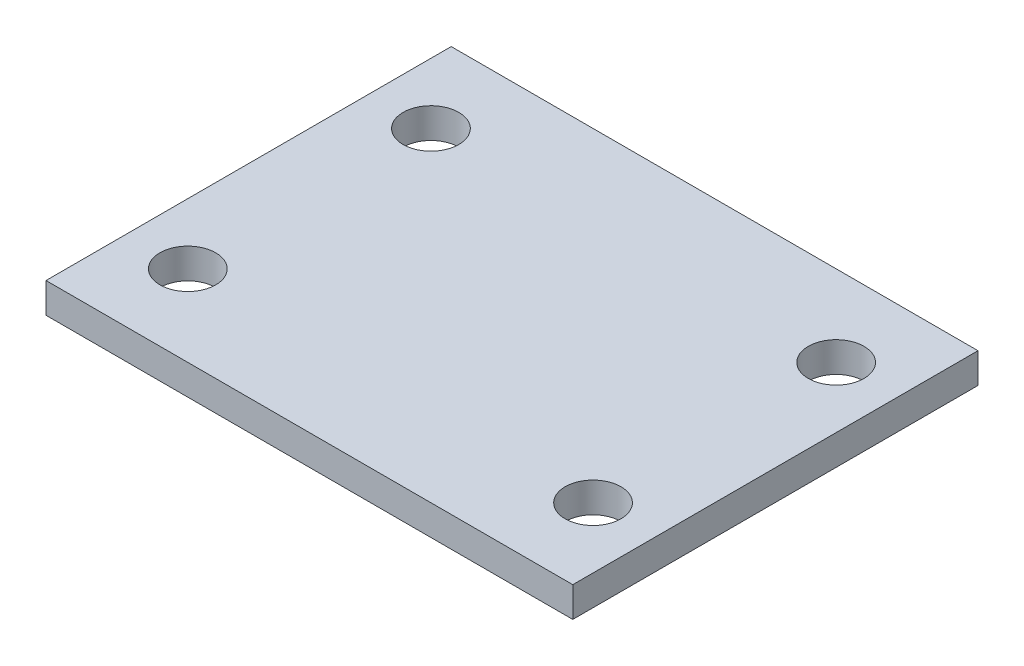
SolidWorks part; units mm, degrees
ref_plane "Front Plane" through (0, 0, 0) normal (0, 0, 1) x (1, 0, 0)
ref_plane "Top Plane" through (0, 0, 0) normal (0, 1, 0) x (1, 0, 0)
ref_plane "Right Plane" through (0, 0, 0) normal (1, 0, 0) x (0, 0, -1)
sketch "Sketch1" plane through (0, 0, 0) normal (0, 1, 0) x (1, 0, 0)
  line L1 (-26, 20) -> (26, 20)
  line L2 (-26, 20) -> (-26, -20)
  line L3 (-26, -20) -> (26, -20)
  line L4 (26, 20) -> (26, -20)
  line L5 (-26, 20) -> (26, -20) construction
  line L6 (-26, -20) -> (26, 20) construction
  point P0 (0, 0)
  dimension "D1" = 52
  dimension "D2" = 40
extrude "Boss-Extrude1" add sketch "Sketch1" along normal blind 2.9743
hole_wizard "M5 Clearance Hole1" positions "Sketch2" profile "Sketch3" hole size "M5" standard "ANSI Metric" end condition through all
sketch "Sketch2" plane through (0, 0, 0) normal (0, -1, 0) x (-1, 0, 0)
  circle A0 centre (-20, -12) radius 2.1 construction
  circle A1 centre (20, -12) radius 2.1 construction
  circle A2 centre (20, 12) radius 2.1 construction
  circle A3 centre (-20, 12) radius 2.1 construction
  circle A4 centre (-20, -12) radius 2.1 construction
  circle A5 centre (20, -12) radius 2.1 construction
  circle A6 centre (20, 12) radius 2.1 construction
  circle A7 centre (-20, 12) radius 2.1 construction
  point P18 (-20, 12)
  point P21 (20, 12)
  point P24 (20, -12)
  point P27 (-20, -12)
sketch "Sketch3" plane through (20, 0, 12) normal (1, 0, 0) x (0, 0, -1)
  line L0 (0, 0) -> (0, 2.9743)
  line L1 (0, 2.9743) -> (2.75, 2.9743)
  line L2 (2.75, 2.9743) -> (2.75, 0)
  line L5 (2.75, 0) -> (0, 0)
  line L11 (0, -6.35) -> (0, 107.95) construction
  dimension "Thru Hole Dia." = 5.5
  dimension "Thru Hole Depth" = 2.9743
equation "\"length\"= 52mm"
equation "\"width\"= 40mm"
equation "\"thick\"= .1171in"
equation "\"D1@Sketch1\"=\"length\""
equation "\"D2@Sketch1\"=\"width\""
equation "\"D1@Boss-Extrude1\"= \"thick\""
